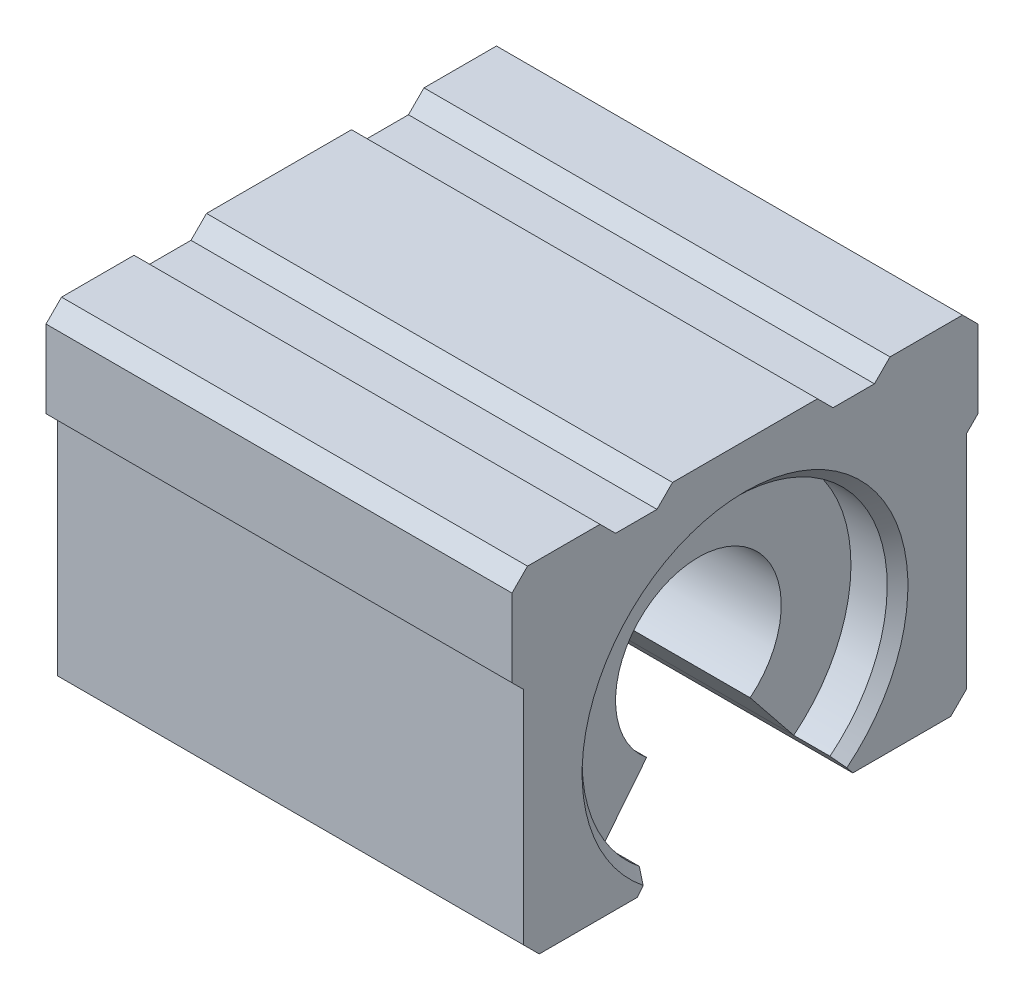
SolidWorks part; units mm, degrees
ref_plane "Front Plane" through (0, 0, 0) normal (0, 0, 1) x (1, 0, 0)
ref_plane "Top Plane" through (0, 0, 0) normal (0, 1, 0) x (1, 0, 0)
ref_plane "Right Plane" through (0, 0, 0) normal (1, 0, 0) x (0, 0, -1)
sketch "Sketch1" plane through (0, 0, 0) normal (1, 0, 0) x (0, 0, -1)
  line L7 (-22.5, 18.5) -> (-21, 20)
  line L8 (22.5, 18.5) -> (21, 20)
  line L9 (-22.5, 11) -> (-21.3686, 9.8686)
  line L10 (-21.3686, 9.8686) -> (-21.3686, -11.5)
  line L11 (22.5, 11) -> (21.3686, 9.8686)
  line L12 (21.3686, 9.8686) -> (21.3686, -11.5)
  line L13 (-22.5, 18.5) -> (-22.5, 11)
  line L14 (22.5, 18.5) -> (22.5, 11)
  line L16 (-21.3686, -11.5) -> (-19.8686, -13)
  line L17 (21.3686, -11.5) -> (19.8686, -13)
  line L18 (10.4083, -13) -> (0, 0) construction
  line L19 (0, 0) -> (-10.4083, -13) construction
  line L20 (-21, 20) -> (-14, 20)
  line L21 (-14, 20) -> (-12.5, 18.5)
  line L22 (-7, 20) -> (-8.5, 18.5)
  line L23 (14, 20) -> (12.5, 18.5)
  line L24 (7, 20) -> (8.5, 18.5)
  line L25 (-12.5, 18.5) -> (-8.5, 18.5)
  line L26 (8.5, 18.5) -> (12.5, 18.5)
  line L27 (-7, 20) -> (7, 20)
  line L28 (14, 20) -> (21, 20)
  line L29 (9.2074, -11.5) -> (10.4083, -13)
  line L30 (-10.4083, -13) -> (-9.2074, -11.5) construction
  line L32 (-10.4083, -13) -> (-9.2074, -11.5)
  line L33 (19.8686, -13) -> (10.4083, -13)
  line L34 (-10.4083, -13) -> (-19.8686, -13)
  line L35 (9.2074, -11.5) -> (-9.2074, -11.5)
  arc A0 (10.4083, -13) -> (-10.4083, -13) centre (0, 0) ccw construction
  circle A1 centre (0, 0) radius 8 construction
  arc A2 (9.2074, -11.5) -> (-9.2074, -11.5) centre (0, 0) ccw construction
  point P3 (-22.5, 11)
  point P6 (0, 0)
  point P7 (-22.5, 20)
  point P8 (22.5, 20)
  point P11 (-21.3686, -13)
  point P21 (21.3686, -13)
  point P23 (-5, -6.245)
  point P24 (5, -6.245)
  point P25 (-7, 20)
  point P28 (0, 20)
  point P29 (7, 20)
  dimension "D6" = 21.3686
  dimension "D10" = 16
  dimension "D13" = 10
  dimension "D2" = 9
  dimension "D3" = 45
  dimension "D5" = 42.7373
  dimension "D14" = 28
  dimension "D15" = 7
  dimension "D16" = 7
extrude "Boss-Extrude1" add sketch "Sketch1" along normal blind 45 contours L13 L9 L10 L16 L34 L32 L35 L29 L33 L17 L12 L11 L14 L8 L28 L23 L26 L24 L27 L22 L25 L21 L20 L7
sketch "Sketch8" plane through (0, 0, 0) normal (-1, 0, 0) x (0, 0, 1)
  line L0 (-9.2074, -11.5) -> (9.2074, -11.5)
  arc A0 (9.2074, -11.5) -> (-9.2074, -11.5) centre (0, 0) ccw
extrude "Cut-Extrude1" cut sketch "Sketch8" against normal blind 4.5 contours A0 L0
sketch "Sketch9" plane through (45, 0, 0) normal (1, 0, 0) x (0, 0, -1)
  line L0 (-9.2074, -11.5) -> (9.2074, -11.5)
  arc A0 (9.2074, -11.5) -> (-9.2074, -11.5) centre (0, 0) ccw
extrude "Cut-Extrude2" cut sketch "Sketch9" against normal blind 4.5
chamfer "Chamfer3" distance 1 angle 45 1 edges at (45, 14.7318, 0)
chamfer "Chamfer4" distance 1 angle 45 1 edges at (0, 14.7318, 0)
sketch "Sketch10" plane through (40.5, 0, 0) normal (1, 0, 0) x (0, 0, -1)
  line L0 (-9.2074, -11.5) -> (-5, -6.245)
  line L1 (4.9939, -6.2498) -> (9.2074, -11.5)
  arc A1 (-5, -6.245) -> (4.9939, -6.2498) centre (0, 0) cw
  arc A2 (9.2074, -11.5) -> (-9.2074, -11.5) centre (0, 0) ccw
  arc A3 (9.2074, -11.5) -> (-9.2074, -11.5) centre (0, 0) ccw construction
  line M3 (-9.2074, -11.5) -> (9.2074, -11.5)
extrude "Cut-Extrude3" cut sketch "Sketch10" against normal up to surface (36 mm away) contours A1 L0 L1 M3 up to face at (4.5, 1.6159, 0)
